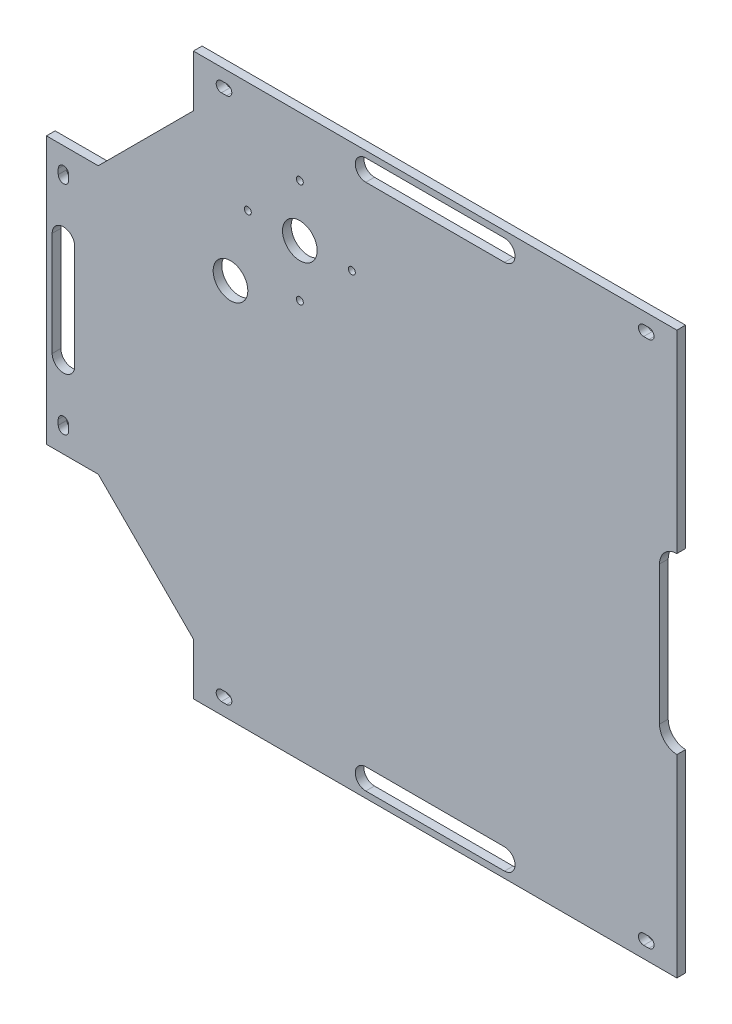
SolidWorks part; units mm, degrees
ref_plane "Front Plane" through (0, 0, 0) normal (0, 0, 1) x (1, 0, 0)
ref_plane "Top Plane" through (0, 0, 0) normal (0, 1, 0) x (1, 0, 0)
ref_plane "Right Plane" through (0, 0, 0) normal (1, 0, 0) x (0, 0, -1)
sketch "Sketch2" plane through (0, 0, 0) normal (0, 0, 1) x (1, 0, 0)
  line L0 (-130.7031, -382.3142) -> (-100.7031, -382.3142)
  line L1 (-100.7031, -382.3142) -> (-45.9544, -327.5654)
  line L2 (-45.9544, -327.5654) -> (-45.9544, -297.5654)
  line L3 (-45.9544, -297.5654) -> (233.2969, -297.5654)
  line L4 (-130.7031, -382.3142) -> (-130.7031, -536.8167)
  line L5 (-130.7031, -536.8167) -> (-100.7031, -536.8167)
  line L6 (-100.7031, -536.8167) -> (-45.9544, -591.5654)
  line L7 (-45.9544, -591.5654) -> (-45.9544, -621.5654)
  line L8 (-45.9544, -621.5654) -> (233.2969, -621.5654)
  line L9 (233.2969, -621.5654) -> (233.2969, -509.5654)
  line L10 (-120.7031, -429.5654) -> (-120.7031, -489.5654) construction
  line L12 (223.2969, -419.5654) -> (223.2969, -499.5654)
  line L13 (233.2969, -409.5654) -> (233.2969, -297.5654)
  line L17 (-29.5963, -307.5247) -> (-26.5963, -307.5247) construction
  line L21 (-29.5963, -304.5247) -> (-26.5963, -304.5247)
  line L24 (-114.2031, -429.5654) -> (-114.2031, -489.5654)
  line L25 (-29.5963, -310.5247) -> (-26.5963, -310.5247)
  line L28 (216.9387, -307.5247) -> (213.9387, -307.5247) construction
  line L31 (216.9387, -304.5247) -> (213.9387, -304.5247)
  line L34 (-127.2031, -429.5654) -> (-127.2031, -489.5654)
  line L37 (53.6712, -307.5247) -> (133.6712, -307.5247) construction
  line L42 (216.9387, -310.5247) -> (213.9387, -310.5247)
  line L43 (216.9387, -611.6062) -> (213.9387, -611.6062) construction
  line L44 (216.9387, -614.6062) -> (213.9387, -614.6062)
  line L45 (216.9387, -608.6062) -> (213.9387, -608.6062)
  line L46 (-29.5963, -611.6062) -> (-26.5963, -611.6062) construction
  line L47 (-29.5963, -614.6062) -> (-26.5963, -614.6062)
  line L48 (-29.5963, -608.6062) -> (-26.5963, -608.6062)
  line L50 (-120.7031, -395.4737) -> (-120.7031, -398.4737) construction
  line L51 (-117.7031, -395.4737) -> (-117.7031, -398.4737)
  line L52 (-123.7031, -395.4737) -> (-123.7031, -398.4737)
  line L53 (53.6712, -301.4531) -> (133.6712, -301.4531)
  line L54 (-120.7031, -523.6571) -> (-120.7031, -520.6571) construction
  line L55 (-117.7031, -523.6571) -> (-117.7031, -520.6571)
  line L56 (-123.7031, -523.6571) -> (-123.7031, -520.6571)
  line L57 (53.6712, -313.5962) -> (133.6712, -313.5962)
  line L59 (53.6712, -611.6062) -> (133.6712, -611.6062) construction
  line L60 (53.6712, -617.6777) -> (133.6712, -617.6777)
  line L61 (53.6712, -605.5347) -> (133.6712, -605.5347)
  arc A0 (233.2969, -409.5654) -> (223.2969, -419.5654) centre (233.2969, -419.5654) ccw
  arc A1 (223.2969, -499.5654) -> (233.2969, -509.5654) centre (233.2969, -499.5654) ccw
  circle A21 centre (15.6336, -331.7945) radius 2
  circle A22 centre (-14.3664, -361.7945) radius 2
  circle A23 centre (15.6336, -391.7945) radius 2
  circle A24 centre (45.6336, -361.7945) radius 2
  circle A25 centre (15.6336, -361.7945) radius 10
  circle A26 centre (-24.3664, -401.7945) radius 10
  arc A27 (-29.5963, -304.5247) -> (-29.5963, -310.5247) centre (-29.5963, -307.5247) ccw
  arc A28 (-26.5963, -310.5247) -> (-26.5963, -304.5247) centre (-26.5963, -307.5247) ccw
  arc A29 (216.9387, -304.5247) -> (216.9387, -310.5247) centre (216.9387, -307.5247) cw
  arc A30 (213.9387, -310.5247) -> (213.9387, -304.5247) centre (213.9387, -307.5247) cw
  arc A31 (216.9387, -614.6062) -> (216.9387, -608.6062) centre (216.9387, -611.6062) ccw
  arc A32 (213.9387, -608.6062) -> (213.9387, -614.6062) centre (213.9387, -611.6062) ccw
  arc A33 (-29.5963, -614.6062) -> (-29.5963, -608.6062) centre (-29.5963, -611.6062) cw
  arc A34 (-26.5963, -608.6062) -> (-26.5963, -614.6062) centre (-26.5963, -611.6062) cw
  arc A35 (-117.7031, -395.4737) -> (-123.7031, -395.4737) centre (-120.7031, -395.4737) ccw
  arc A36 (-123.7031, -398.4737) -> (-117.7031, -398.4737) centre (-120.7031, -398.4737) ccw
  arc A37 (-117.7031, -523.6571) -> (-123.7031, -523.6571) centre (-120.7031, -523.6571) cw
  arc A38 (-123.7031, -520.6571) -> (-117.7031, -520.6571) centre (-120.7031, -520.6571) cw
  arc A39 (-114.2031, -429.5654) -> (-127.2031, -429.5654) centre (-120.7031, -429.5654) ccw
  arc A40 (-127.2031, -489.5654) -> (-114.2031, -489.5654) centre (-120.7031, -489.5654) ccw
  arc A41 (53.6712, -301.4531) -> (53.6712, -313.5962) centre (53.6712, -307.5247) ccw
  arc A42 (133.6712, -313.5962) -> (133.6712, -301.4531) centre (133.6712, -307.5247) ccw
  arc A43 (53.6712, -617.6777) -> (53.6712, -605.5347) centre (53.6712, -611.6062) cw
  arc A44 (133.6712, -605.5347) -> (133.6712, -617.6777) centre (133.6712, -611.6062) cw
  point P12 (233.2969, -459.5654)
  point P19 (-28.0963, -307.5247)
  point P28 (215.4387, -307.5247)
  point P32 (-120.7031, -459.5654)
  point P37 (215.4387, -611.6062)
  point P46 (-28.0963, -611.6062)
  point P53 (-120.7031, -396.9737)
  point P62 (-120.7031, -522.1571)
  point P66 (93.6712, -307.5247)
  point P75 (93.6712, -611.6062)
extrude "Boss-Extrude6" add sketch "Sketch2" along normal blind 5
sketch "Sketch5" plane through (0, 0, 5) normal (0, 0, 1) x (1, 0, 0)
  line L0 (-45.7544, -327.6483) -> (-100.6203, -382.5142)
  line L1 (-100.6203, -382.5142) -> (-130.5031, -382.5142)
  line L2 (-130.5031, -382.5142) -> (-130.5031, -536.6167)
  line L3 (-130.5031, -536.6167) -> (-100.6203, -536.6167)
  line L4 (-100.6203, -536.6167) -> (-45.7544, -591.4826)
  line L5 (-45.7544, -591.4826) -> (-45.7544, -621.3654)
  line L6 (-45.7544, -621.3654) -> (233.0969, -621.3654)
  line L7 (233.0969, -621.3654) -> (233.0969, -509.7635)
  line L8 (223.0969, -499.5654) -> (223.0969, -419.5654)
  line L9 (233.0969, -409.3674) -> (233.0969, -297.7654)
  line L10 (233.0969, -297.7654) -> (-45.7544, -297.7654)
  line L11 (-45.7544, -297.7654) -> (-45.7544, -327.6483)
  line L12 (-130.7031, -382.3142) -> (-130.7031, -536.8167)
  line L13 (-130.7031, -536.8167) -> (-100.7031, -536.8167)
  line L14 (-100.7031, -536.8167) -> (-45.9544, -591.5654)
  line L15 (-45.9544, -591.5654) -> (-45.9544, -621.5654)
  line L16 (-45.9544, -621.5654) -> (233.2969, -621.5654)
  line L17 (233.2969, -621.5654) -> (233.2969, -509.5654)
  line L18 (223.2969, -499.5654) -> (223.2969, -419.5654)
  line L19 (233.2969, -409.5654) -> (233.2969, -297.5654)
  line L20 (233.2969, -297.5654) -> (-45.9544, -297.5654)
  line L21 (-45.9544, -297.5654) -> (-45.9544, -327.5654)
  line L22 (-45.9544, -327.5654) -> (-100.7031, -382.3142)
  line L23 (-100.7031, -382.3142) -> (-130.7031, -382.3142)
  line L24 (-130.7031, -382.3142) -> (-130.7031, -536.8167)
  line L25 (-130.7031, -536.8167) -> (-100.7031, -536.8167)
  line L26 (-100.7031, -536.8167) -> (-45.9544, -591.5654)
  line L27 (-45.9544, -591.5654) -> (-45.9544, -621.5654)
  line L28 (-45.9544, -621.5654) -> (233.2969, -621.5654)
  line L29 (233.2969, -621.5654) -> (233.2969, -509.5654)
  line L30 (223.2969, -499.5654) -> (223.2969, -419.5654)
  line L31 (233.2969, -409.5654) -> (233.2969, -297.5654)
  line L32 (233.2969, -297.5654) -> (-45.9544, -297.5654)
  line L33 (-45.9544, -297.5654) -> (-45.9544, -327.5654)
  line L34 (-45.9544, -327.5654) -> (-100.7031, -382.3142)
  line L35 (-100.7031, -382.3142) -> (-130.7031, -382.3142)
  arc A0 (223.0969, -499.5654) -> (233.0969, -509.7635) centre (233.2969, -499.5654) ccw
  arc A1 (233.0969, -409.3674) -> (223.0969, -419.5654) centre (233.2969, -419.5654) ccw
  arc A2 (223.2969, -499.5654) -> (233.2969, -509.5654) centre (233.2969, -499.5654) ccw
  arc A3 (233.2969, -409.5654) -> (223.2969, -419.5654) centre (233.2969, -419.5654) ccw
  arc A4 (223.2969, -499.5654) -> (233.2969, -509.5654) centre (233.2969, -499.5654) ccw
  arc A5 (233.2969, -409.5654) -> (223.2969, -419.5654) centre (233.2969, -419.5654) ccw
  dimension "D1" = 0
  dimension "D2" = 0.2
extrude "Cut-Extrude9" cut sketch "Sketch5" against normal blind 10
